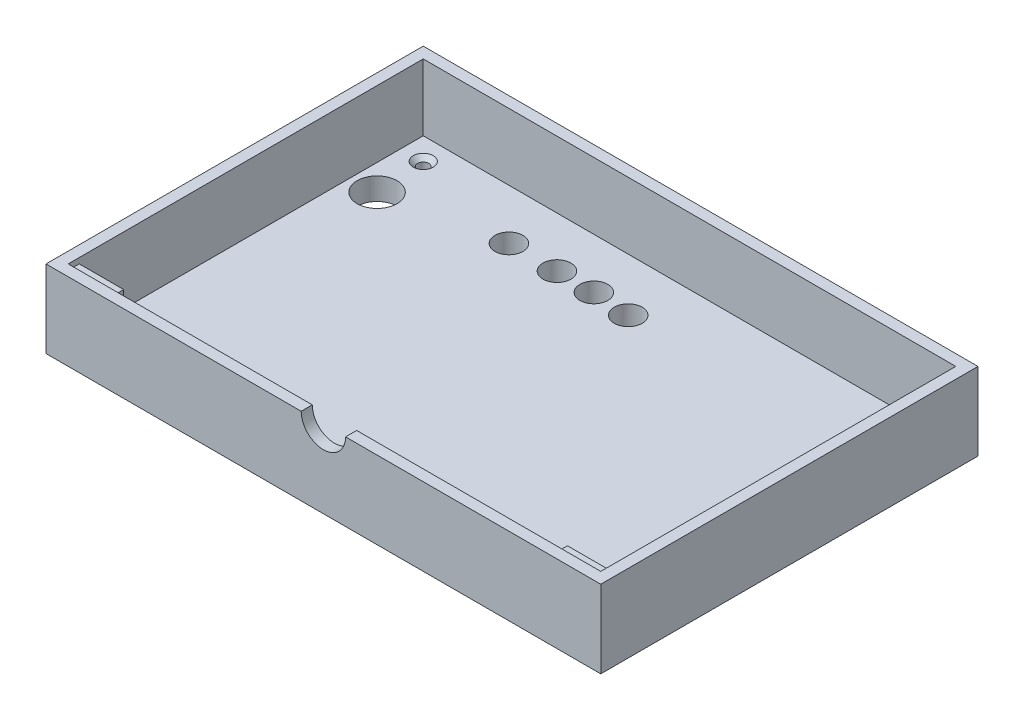
SolidWorks part; units mm, degrees
ref_plane "Front Plane" through (0, 0, 0) normal (0, 0, 1) x (1, 0, 0)
ref_plane "Top Plane" through (0, 0, 0) normal (0, 1, 0) x (1, 0, 0)
ref_plane "Right Plane" through (0, 0, 0) normal (1, 0, 0) x (0, 0, -1)
sketch "Sketch1" plane through (0, 0, 0) normal (0, 1, 0) x (1, 0, 0)
  line L1 (152.4, -101.6) -> (-152.4, -101.6)
  line L2 (152.4, -101.6) -> (152.4, 101.6)
  line L3 (152.4, 101.6) -> (-152.4, 101.6)
  line L4 (-152.4, -101.6) -> (-152.4, 101.6)
  line L5 (152.4, -101.6) -> (-152.4, 101.6) construction
  line L6 (152.4, 101.6) -> (-152.4, -101.6) construction
  point P0 (0, 0)
  dimension "D1" = 304.8
  dimension "D2" = 203.2
extrude "Boss-Extrude1" add sketch "Sketch1" along normal blind 6.35 contours L3 L4 L1 L2
sketch "Sketch2" plane through (0, 6.35, 0) normal (0, 1, 0) x (1, 0, 0)
  line L0 (152.4, 101.6) -> (-152.4, 101.6) construction
  line L1 (158.75, -107.95) -> (-158.75, -107.95)
  line L2 (158.75, -107.95) -> (158.75, 107.95)
  line L3 (158.75, 107.95) -> (-158.75, 107.95)
  line L4 (-158.75, -107.95) -> (-158.75, 107.95)
  line L5 (158.75, -107.95) -> (-158.75, 107.95) construction
  line L6 (158.75, 107.95) -> (-158.75, -107.95) construction
  line L7 (-152.4, -101.6) -> (-152.4, 101.6) construction
  point P0 (0, 0)
  dimension "D1" = 6.35
  dimension "D2" = 6.35
extrude "Boss-Extrude2" add sketch "Sketch2" along normal blind 6.35
sketch "Sketch3" plane through (0, 12.7, 0) normal (0, 1, 0) x (1, 0, 0)
  line L0 (0, -76.2) -> (0, 76.2) construction
  line L1 (101.6, 0) -> (-101.6, 0) construction
  line L2 (-141.9451, 91.1451) -> (-137.4549, 86.6549) construction
  line L4 (-158.75, 107.95) -> (-152.4, 107.95) construction
  line L5 (158.75, 107.95) -> (-158.75, 107.95) construction
  line L6 (-152.4, 107.95) -> (-152.4, 101.6) construction
  line L7 (-152.4, 101.6) -> (-127, 101.6) construction
  line L15 (-127, 101.6) -> (-127, 76.2) construction
  line L16 (-127, 76.2) -> (-152.4, 101.6) construction
  line L17 (-145.8077, 82.7923) -> (-133.5923, 95.0077) construction
  circle A0 centre (-139.7, 88.9) radius 3.175
  circle A1 centre (139.7, 88.9) radius 3.175
  circle A2 centre (139.7, -88.9) radius 3.175
  circle A3 centre (-139.7, -88.9) radius 3.175
  point P8 (0, 0)
  point P12 (0, 0)
  point P29 (-139.7, 88.9)
  dimension "D4" = 6.35
  dimension "D2" = 6.35
  dimension "D3" = 25.4
  dimension "D1" = 6.35
  dimension "D5" = 25.4
  dimension "D6" = 0
extrude "Cut-Extrude1" cut sketch "Sketch3" against normal blind 12.7
chamfer "Chamfer1" distance 2.54 angle 45 4 edges at (-139.7, 12.7, 85.725) (139.7, 12.7, -92.075) (139.7, 12.7, 92.075) (-139.7, 12.7, -85.725)
sketch "Sketch5" plane through (0, 12.7, 0) normal (0, 1, 0) x (1, 0, 0)
  line L0 (158.75, 107.95) -> (-158.75, 107.95) construction
  line L1 (152.4, -101.6) -> (-152.4, -101.6)
  line L2 (152.4, -101.6) -> (152.4, 101.6)
  line L3 (152.4, 101.6) -> (-152.4, 101.6)
  line L4 (-152.4, -101.6) -> (-152.4, 101.6)
  line L5 (152.4, -101.6) -> (-152.4, 101.6) construction
  line L6 (152.4, 101.6) -> (-152.4, -101.6) construction
  line L7 (-158.75, 107.95) -> (-158.75, -107.95) construction
  line L8 (0, -101.6) -> (0, 101.6) construction
  line L9 (-152.4, 101.6) -> (-127, 101.6)
  line L10 (-152.4, 101.6) -> (-152.4, 76.2)
  line L11 (-152.4, 76.2) -> (-127, 76.2)
  line L12 (-127, 101.6) -> (-127, 76.2)
  line L13 (152.4, 0) -> (-152.4, 0) construction
  line L14 (152.4, 76.2) -> (127, 76.2)
  line L15 (127, 101.6) -> (127, 76.2)
  line L16 (152.4, 101.6) -> (127, 101.6)
  line L17 (152.4, 101.6) -> (152.4, 76.2)
  line L18 (-152.4, -76.2) -> (-127, -76.2)
  line L19 (-127, -101.6) -> (-127, -76.2)
  line L20 (-152.4, -101.6) -> (-127, -101.6)
  line L21 (-152.4, -101.6) -> (-152.4, -76.2)
  line L22 (152.4, -101.6) -> (127, -101.6)
  line L23 (127, -101.6) -> (127, -76.2)
  line L24 (152.4, -76.2) -> (127, -76.2)
  line L25 (152.4, -101.6) -> (152.4, -76.2)
  point P0 (0, 0)
  point P16 (0, 0)
  point P19 (0, 0)
  dimension "D1" = 6.35
  dimension "D2" = 6.35
  dimension "D3" = 25.4
  dimension "D4" = 25.4
sketch "Sketch6" plane through (0, 12.7, 0) normal (0, 1, 0) x (1, 0, 0)
  line L0 (152.4, -101.6) -> (-152.4, -101.6) construction
  line L1 (152.4, -101.6) -> (152.4, 101.6) construction
  line L2 (152.4, 101.6) -> (-152.4, 101.6) construction
  line L3 (-152.4, -101.6) -> (-152.4, 101.6) construction
  line L4 (152.4, -101.6) -> (-152.4, -101.6)
  line L5 (152.4, -101.6) -> (152.4, 101.6)
  line L6 (152.4, 101.6) -> (-152.4, 101.6)
  line L7 (-152.4, -101.6) -> (-152.4, 101.6)
  line L9 (-158.75, 107.95) -> (158.75, 107.95)
  line L10 (-158.75, 107.95) -> (-158.75, -107.95)
  line L11 (-158.75, -107.95) -> (158.75, -107.95)
  line L12 (158.75, 107.95) -> (158.75, -107.95)
extrude "Boss-Extrude3" add sketch "Sketch6" along normal blind 38.1
sketch "Sketch7" plane through (0, 0, 101.6) normal (0, 0, -1) x (-1, 0, 0)
  line L0 (-152.4, 50.8) -> (-152.4, 12.7) construction
  line L1 (-152.4, 47.625) -> (-127, 47.625)
  line L2 (-152.4, 47.625) -> (-152.4, 41.275)
  line L3 (-152.4, 41.275) -> (-127, 41.275)
  line L4 (-127, 47.625) -> (-127, 41.275)
  line L5 (152.4, 50.8) -> (-152.4, 50.8) construction
  line L6 (0, 12.7) -> (0, 50.8) construction
  line L7 (152.4, 41.275) -> (127, 41.275)
  line L8 (127, 47.625) -> (127, 41.275)
  line L9 (152.4, 47.625) -> (127, 47.625)
  line L10 (152.4, 47.625) -> (152.4, 41.275)
  dimension "D1" = 6.35
  dimension "D2" = 25.4
  dimension "D3" = 3.175
extrude "Boss-Extrude4" add sketch "Sketch7" along normal blind 6.35 separate body
sketch "Sketch8" plane through (0, 0, 107.95) normal (0, 0, 1) x (1, 0, 0)
  line L0 (0, 50.8) -> (0, 6.35) construction
  line L1 (-158.75, 50.8) -> (158.75, 50.8) construction
  line L2 (-158.75, 6.35) -> (158.75, 6.35) construction
  line L3 (-12.7, 50.8) -> (12.7, 50.8)
  arc A0 (12.7, 50.8) -> (-12.7, 50.8) centre (0, 50.8) cw
  dimension "D1" = 12.7
extrude "Cut-Extrude4" cut sketch "Sketch8" against normal blind 6.35 contours A0 L3
sketch "Sketch4" plane through (0, 12.7, 0) normal (0, 1, 0) x (1, 0, 0)
  circle A0 centre (-137.6617, 60.453) radius 11.43
  circle A1 centre (-74.551, 72.7924) radius 8
  circle A2 centre (-47.068, 72.7924) radius 8
  circle A3 centre (-25.9499, 72.7924) radius 8
  circle A4 centre (-4.7966, 71.3076) radius 8
  point P4 (-47.068, 72.7924)
  point P9 (-25.9499, 72.7924)
extrude "Cut-Extrude2" cut sketch "Sketch4" against normal blind 12.7
